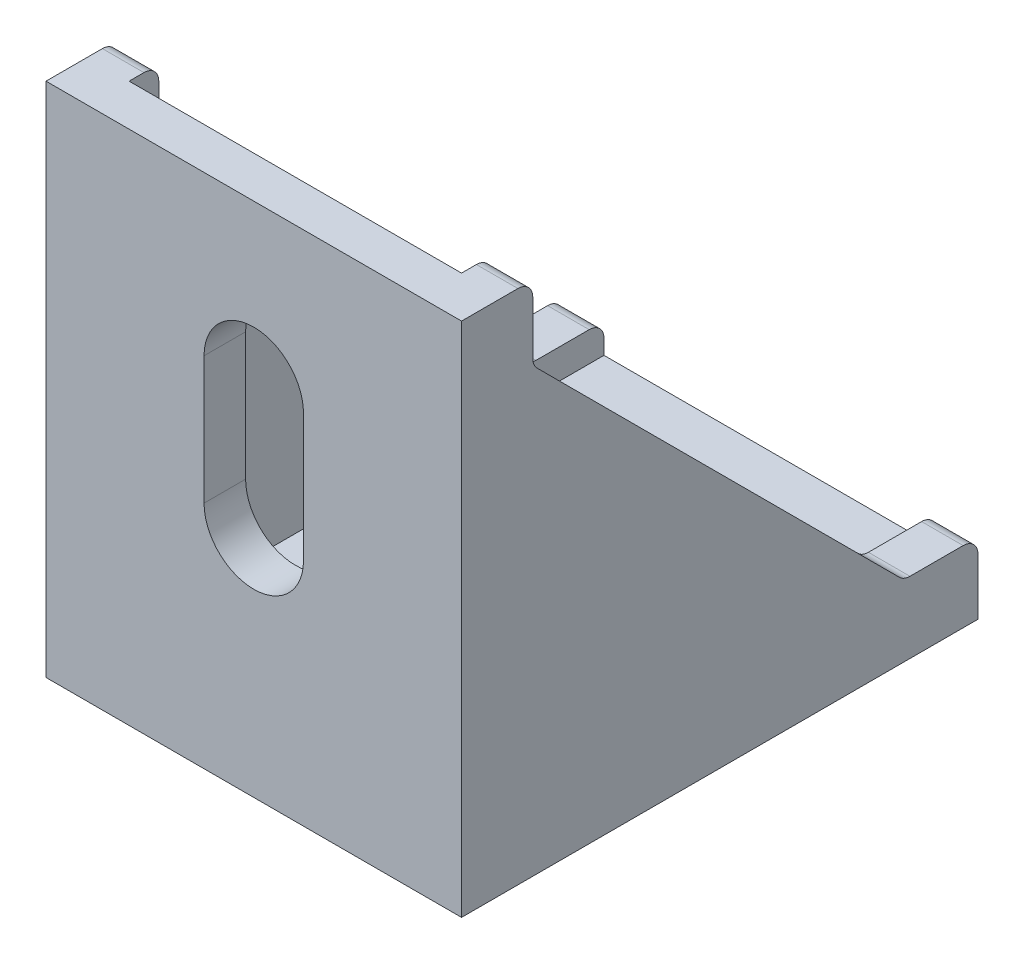
SolidWorks part; units mm, degrees
material "201 退火不锈钢 (SS)"
ref_plane "前视基准面" through (0, 0, 0) normal (0, 0, 1) x (1, 0, 0)
ref_plane "上视基准面" through (0, 0, 0) normal (0, 1, 0) x (1, 0, 0)
ref_plane "右视基准面" through (0, 0, 0) normal (1, 0, 0) x (0, 0, -1)
sketch "草图1" plane through (0, 0, 0) normal (1, 0, 0) x (0, 0, -1)
  line L0 (0, 34.8) -> (0, 0)
  line L1 (0, 0) -> (34.8, 0)
  line L2 (34.8, 0) -> (34.8, 2.8)
  line L3 (34.8, 2.8) -> (2.8, 2.8)
  line L4 (2.8, 2.8) -> (2.8, 34.8)
  line L5 (2.8, 34.8) -> (0, 34.8)
  dimension "D1" = 34.8
  dimension "D2" = 34.8
  dimension "D3" = 2.8
  dimension "D4" = 2.8
extrude "凸台-拉伸1" add sketch "草图1" against normal mid plane 28
sketch "草图2" plane through (14, 0, 0) normal (1, 0, 0) x (0, 0, -1)
  line L0 (2.8, 34.8) -> (4.8, 34.8)
  line L1 (4.8, 34.8) -> (4.8, 29.8)
  line L2 (4.8, 29.8) -> (29.8, 4.8)
  line L3 (29.8, 4.8) -> (34.8, 4.8)
  line L4 (34.8, 4.8) -> (34.8, 2.8)
  line L5 (34.8, 2.8) -> (2.8, 2.8)
  line L6 (2.8, 2.8) -> (2.8, 34.8)
  dimension "D1" = 2
  dimension "D2" = 2
  dimension "D3" = 5
  dimension "D4" = 5
extrude "凸台-拉伸3" add sketch "草图2" against normal blind 2.8
mirror "镜向1" about plane through (0, 0, 0) normal (1, 0, 0) of "凸台-拉伸3"
fillet "圆角1" radius 1 8 edges at (12.6, 29.8, -4.8) (-12.6, 29.8, -4.8) (-12.6, 4.8, -29.8) (12.6, 4.8, -29.8) (12.6, 4.8, -34.8) (-12.6, 4.8, -34.8) (-12.6, 34.8, -4.8) (12.6, 34.8, -4.8)
sketch "草图3" plane through (0, 2.8, 0) normal (0, 1, 0) x (1, 0, 0)
  line L0 (0, 15.5) -> (0, 24.1) construction
  line L1 (-3.35, 15.5) -> (-3.35, 24.1)
  line L2 (3.35, 15.5) -> (3.35, 24.1)
  line L3 (-11.2, 34.8) -> (11.2, 34.8) construction
  arc A0 (-3.35, 15.5) -> (3.35, 15.5) centre (0, 15.5) ccw
  arc A1 (3.35, 24.1) -> (-3.35, 24.1) centre (0, 24.1) ccw
  point P3 (0, 19.8)
  dimension "D1" = 3.35
  dimension "D2" = 15
extrude "切除-拉伸1" cut sketch "草图3" against normal blind 2.8
sketch "草图4" plane through (0, 0, -2.8) normal (0, 0, -1) x (-1, 0, 0)
  line L0 (0, 15.5) -> (0, 24.1) construction
  line L1 (-3.35, 15.5) -> (-3.35, 24.1)
  line L2 (3.35, 15.5) -> (3.35, 24.1)
  line L3 (11.2, 34.8) -> (-11.2, 34.8) construction
  arc A0 (-3.35, 15.5) -> (3.35, 15.5) centre (0, 15.5) ccw
  arc A1 (3.35, 24.1) -> (-3.35, 24.1) centre (0, 24.1) ccw
  point P3 (0, 19.8)
  dimension "D1" = 15
extrude "切除-拉伸2" cut sketch "草图4" against normal blind 2.8
